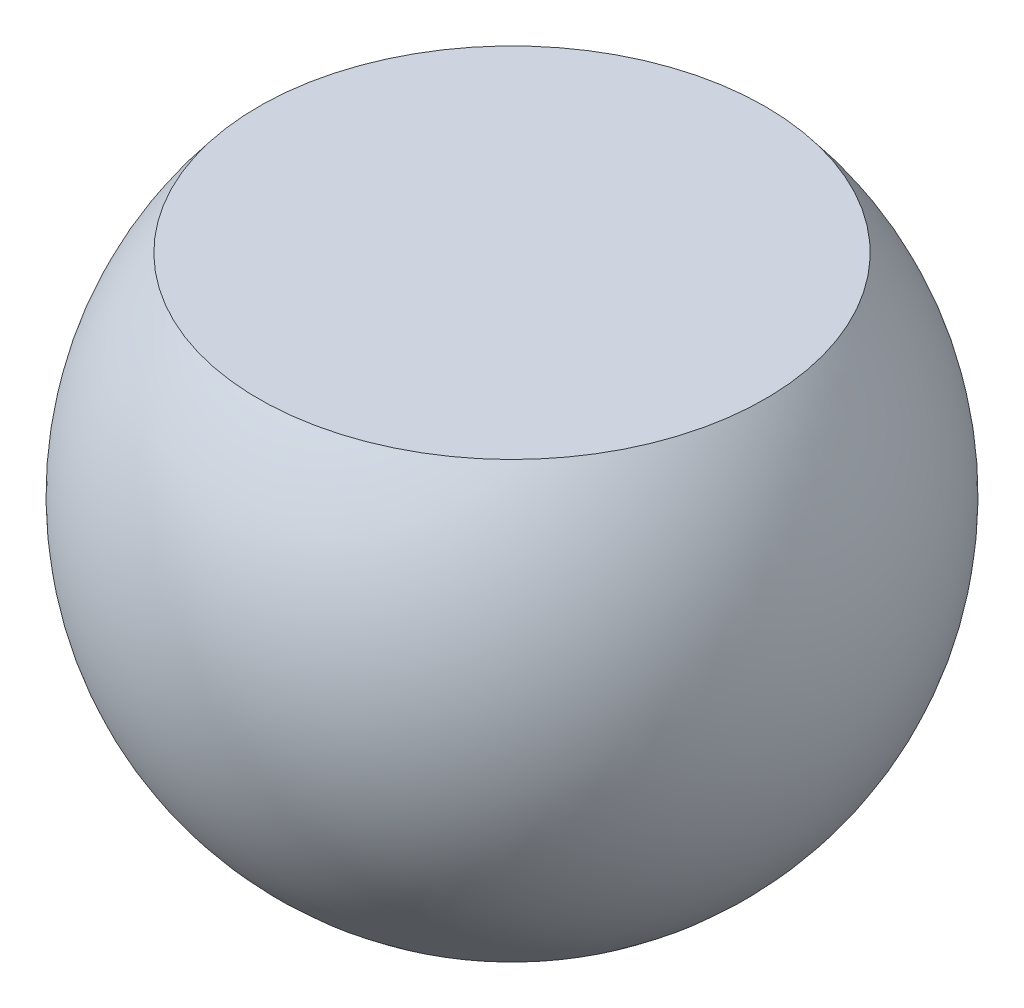
SolidWorks part; units mm, degrees
ref_plane "Front Plane" through (0, 0, 0) normal (0, 0, 1) x (1, 0, 0)
ref_plane "Top Plane" through (0, 0, 0) normal (0, 1, 0) x (1, 0, 0)
ref_plane "Right Plane" through (0, 0, 0) normal (1, 0, 0) x (0, 0, -1)
sketch "Sketch1" plane through (0, 0, 0) normal (0, 1, 0) x (1, 0, 0)
  line L0 (0, 3.37) -> (0, -3.37)
  arc A0 (0, 3.37) -> (0, -3.37) centre (0, 0) ccw
  dimension "D1" = 6.74
revolve "Revolve2" add sketch "Sketch1" angle 360 about L0
ref_plane "Plane1" through (0, 2.156, 0) normal (0, 1, 0) x (1, 0, 0)
sketch "Sketch3" plane through (0, 2.156, 0) normal (0, 1, 0) x (1, 0, 0)
  line L1 (4.216, 4.1288) -> (-4.216, 4.1288)
  line L2 (4.216, 4.1288) -> (4.216, -4.1288)
  line L3 (4.216, -4.1288) -> (-4.216, -4.1288)
  line L4 (-4.216, 4.1288) -> (-4.216, -4.1288)
  line L5 (4.216, 4.1288) -> (-4.216, -4.1288) construction
  line L6 (4.216, -4.1288) -> (-4.216, 4.1288) construction
  point P0 (0, 0)
extrude "Cut-Extrude1" cut sketch "Sketch3" along normal blind 2.54
